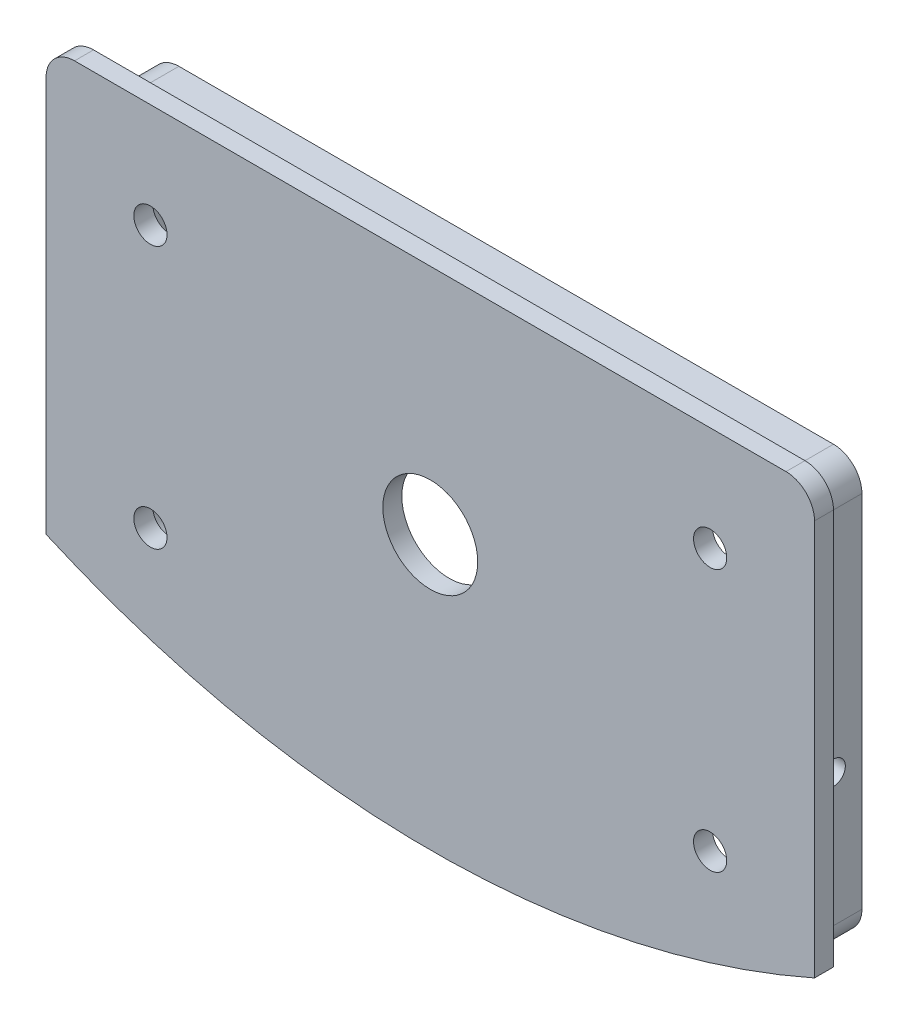
SolidWorks part; units mm, degrees
ref_plane "Płaszczyzna przednia" through (0, 0, 0) normal (0, 0, 1) x (1, 0, 0)
ref_plane "Płaszczyzna górna" through (0, 0, 0) normal (0, 1, 0) x (1, 0, 0)
ref_plane "Płaszczyzna prawa" through (0, 0, 0) normal (1, 0, 0) x (0, 0, -1)
sketch "Szkic1" plane through (0, 0, 0) normal (0, 0, 1) x (1, 0, 0)
  line L1 (-37.5, 21.5) -> (37.5, 21.5)
  line L2 (-37.5, 21.5) -> (-37.5, -21.5)
  line L4 (37.5, 21.5) -> (37.5, -21.5)
  line L5 (-37.5, 21.5) -> (37.5, -21.5) construction
  line L6 (-37.5, -21.5) -> (37.5, 21.5) construction
  arc A0 (-37.5, -21.5) -> (37.5, -21.5) centre (0, 71.2025) ccw
  point P0 (0, 0)
  dimension "D3" = 100
  dimension "D1" = 75
  dimension "D2" = 43
extrude "Dodanie-wyciągnięcie1" add sketch "Szkic1" along normal blind 6
sketch "Szkic2" plane through (0, 0, 6) normal (0, 0, 1) x (1, 0, 0)
  line L0 (-40.5, -20.2292) -> (-40.5, 21.5)
  line L1 (40.5, 21.5) -> (40.5, -20.2292)
  line L3 (-37.5, 21.5) -> (-37.5, -21.5) construction
  line L4 (37.5, -21.5) -> (37.5, 21.5) construction
  line L6 (40.5, -23.501) -> (40.5, 24.5)
  line L7 (40.5, 24.5) -> (-40.5, 24.5)
  line L8 (-40.5, 24.5) -> (-40.5, -23.501)
  line L10 (37.5, 24.5) -> (-37.5, 24.5)
  arc A0 (-37.5, -21.5) -> (37.5, -21.5) centre (0, 71.2025) ccw construction
  arc A1 (40.5, 21.5) -> (37.5, 24.5) centre (37.5, 21.5) ccw
  arc A2 (-40.5, -23.501) -> (40.5, -23.501) centre (0, 71.2025) ccw
  arc A4 (-40.5, -20.2292) -> (40.5, -20.2292) centre (0, 71.2025) ccw
  arc A5 (-37.5, 24.5) -> (-40.5, 21.5) centre (-37.5, 21.5) ccw
  dimension "D4" = 100
  dimension "D5" = 3
  dimension "D2" = 3
  dimension "D3" = 3
  dimension "D1" = 3
extrude "Dodanie-wyciągnięcie2" add sketch "Szkic2" along normal blind 2 contours A5 L0 A4 L1 A1 L10
shell "Skorupa1" thickness 2
sketch "Szkic3" plane through (0, 0, 6) normal (0, 0, -1) x (-1, 0, 0)
  line L0 (0, 30.2757) -> (0, -34.8179) construction
  line L1 (-54.2447, 13.5) -> (54.2447, 13.5) construction
  line L2 (-54.2447, -14.1416) -> (54.2447, -14.1416) construction
  line L3 (-35.5, 19.5) -> (35.5, 19.5) construction
  line L4 (-35.5, 19.5) -> (-35.5, -20.1416) construction
  line L5 (35.5, 19.5) -> (35.5, -20.1416) construction
  circle A0 centre (-29.5, 13.5) radius 1.75
  circle A1 centre (29.5, 13.5) radius 1.75
  circle A2 centre (29.5, -14.1416) radius 1.75
  circle A3 centre (-29.5, -14.1416) radius 1.75
  circle A4 centre (0, 0) radius 5
  dimension "D3" = 3.5
  dimension "D4" = 3.5
  dimension "D5" = 3.5
  dimension "D6" = 3.5
  dimension "D11" = 10
  dimension "D1" = 6
  dimension "D2" = 6
  dimension "D7" = 6
  dimension "D8" = 6
  dimension "D9" = 6
  dimension "D10" = 6
extrude "Wytnij-wyciągnięcie1" cut sketch "Szkic3" against normal up to surface (2 mm away) up to face at (0, 7.3693, 8)
fillet "Zaokrąglenie1" radius 3 8 edges at (-37.5, -21.5, 3) (37.5, -21.5, 3) (-35.5, -20.1416, 3) (35.5, -20.1416, 3) (35.5, 19.5, 3) (-35.5, 19.5, 3) (-37.5, 21.5, 3) (37.5, 21.5, 3)
fillet "Zaokrąglenie2" radius 2 8 edges at (34.6213, 18.6213, 6) (0, 19.5, 6) (-34.6213, 18.6213, 6) (-35.5, -0.7827, 6) (-34.9575, -19.786, 6) (0, -26.7975, 6) (34.9575, -19.786, 6) (35.5, -0.7827, 6)
sketch "Szkic4" plane through (-37.5, 0, 0) normal (-1, 0, 0) x (0, 0, 1)
  circle A0 centre (3, -5.5) radius 1.25
  dimension "D1" = 2.5
extrude "Wytnij-wyciągnięcie2" cut sketch "Szkic4" against normal up to surface (75 mm away) up to face at (37.5, -0.4774, 3)
